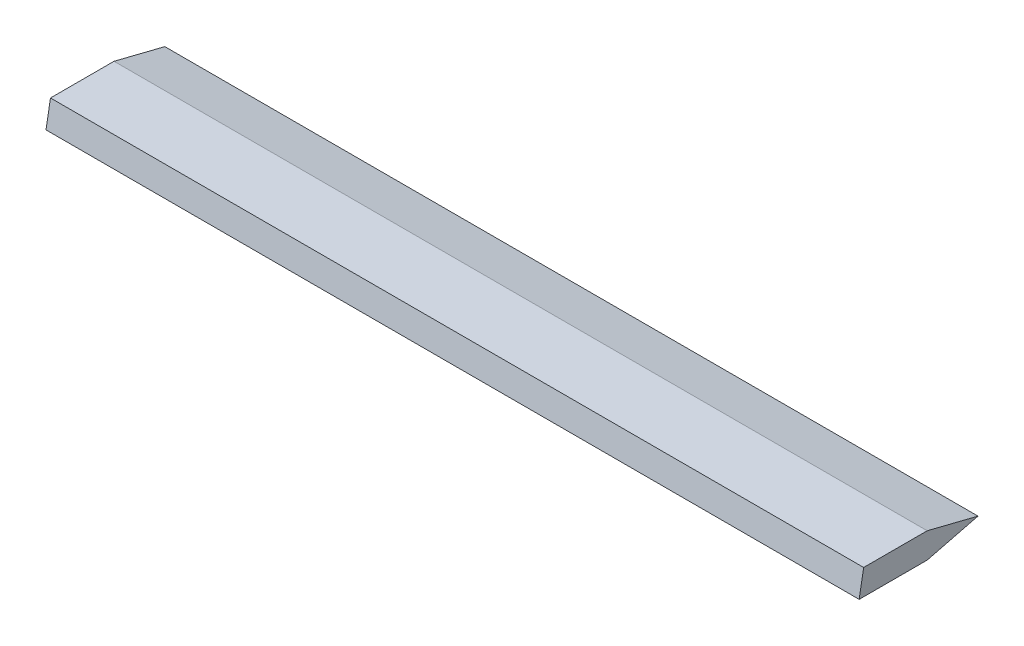
SolidWorks part; units mm, degrees
material "PS HI"
ref_plane "Front Plane" through (0, 0, 0) normal (0, 0, 1) x (1, 0, 0)
ref_plane "Top Plane" through (0, 0, 0) normal (0, 1, 0) x (1, 0, 0)
ref_plane "Right Plane" through (0, 0, 0) normal (1, 0, 0) x (0, 0, -1)
sketch "Sketch1" plane through (0, 0, 0) normal (1, 0, 0) x (0, 0, -1)
  line L0 (0, 0) -> (6.35, 0)
  line L1 (6.35, 0) -> (11.43, -1.27)
  line L2 (11.43, -1.27) -> (6.35, -2.54)
  line L3 (6.35, -2.54) -> (-0.4479, -2.54)
  line L4 (-0.4479, -2.54) -> (0, 0)
  line L5 (0, 0) -> (0, -2.54) construction
  dimension "D1" = 6.35
  dimension "D2" = 5.08
  dimension "D3" = 5.08
  dimension "D4" = 10
  dimension "D5" = 1.27
  dimension "D6" = 1.27
extrude "Boss-Extrude1" add sketch "Sketch1" along normal blind 81.28
